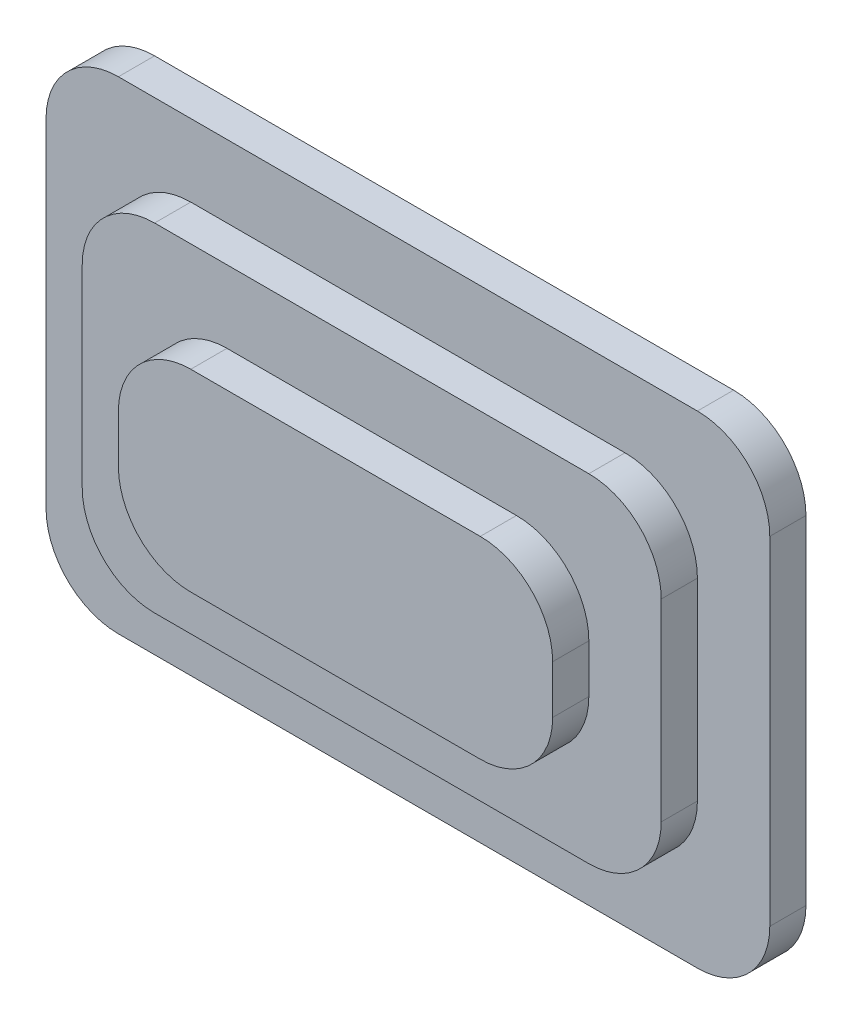
SolidWorks part; units mm, degrees
ref_plane "Front Plane" through (0, 0, 0) normal (0, 0, 1) x (1, 0, 0)
ref_plane "Top Plane" through (0, 0, 0) normal (0, 1, 0) x (1, 0, 0)
ref_plane "Right Plane" through (0, 0, 0) normal (1, 0, 0) x (0, 0, -1)
sketch "Sketch2" plane through (0, 0, 0) normal (0, 0, 1) x (1, 0, 0)
  line L1 (-150, 100) -> (150, 100)
  line L2 (-150, 100) -> (-150, -100)
  line L3 (-150, -100) -> (150, -100)
  line L4 (150, 100) -> (150, -100)
  line L5 (-150, 100) -> (150, -100) construction
  line L6 (-150, -100) -> (150, 100) construction
  point P0 (0, 0)
  dimension "D1" = 300
  dimension "D2" = 200
extrude "Boss-Extrude1" add sketch "Sketch2" along normal blind 15
sketch "Sketch3" plane through (0, 0, 15) normal (0, 0, 1) x (1, 0, 0)
  line L14 (-120, -70) -> (120, -70)
  line L15 (120, -70) -> (120, 70)
  line L16 (-120, 70) -> (-120, -70)
  line L17 (120, 70) -> (-120, 70)
  line L18 (-120, -70) -> (120, -70)
  line L19 (120, -70) -> (120, 70)
  line L20 (-120, 70) -> (-120, -70)
  line L21 (120, 70) -> (-120, 70)
  dimension "D1" = 30
extrude "Boss-Extrude2" add sketch "Sketch3" along normal blind 15
sketch "Sketch4" plane through (0, 0, 30) normal (0, 0, 1) x (1, 0, 0)
  line L14 (-90, -40) -> (90, -40)
  line L15 (90, -40) -> (90, 40)
  line L16 (90, 40) -> (-90, 40)
  line L17 (-90, 40) -> (-90, -40)
  line L18 (-90, -40) -> (90, -40)
  line L19 (90, -40) -> (90, 40)
  line L20 (90, 40) -> (-90, 40)
  line L21 (-90, 40) -> (-90, -40)
  dimension "D1" = 30
extrude "Boss-Extrude3" add sketch "Sketch4" along normal blind 15
fillet "Fillet1" radius 30 4 edges at (90, -40, 37.5) (-90, -40, 37.5) (-90, 40, 37.5) (90, 40, 37.5)
fillet "Fillet2" radius 30 4 edges at (120, -70, 22.5) (-120, -70, 22.5) (-120, 70, 22.5) (120, 70, 22.5)
fillet "Fillet3" radius 30 4 edges at (-150, -100, 7.5) (-150, 100, 7.5) (150, 100, 7.5) (150, -100, 7.5)
scale "Scale2" scale about centroid uniform scaling yes scale factor 2.5
